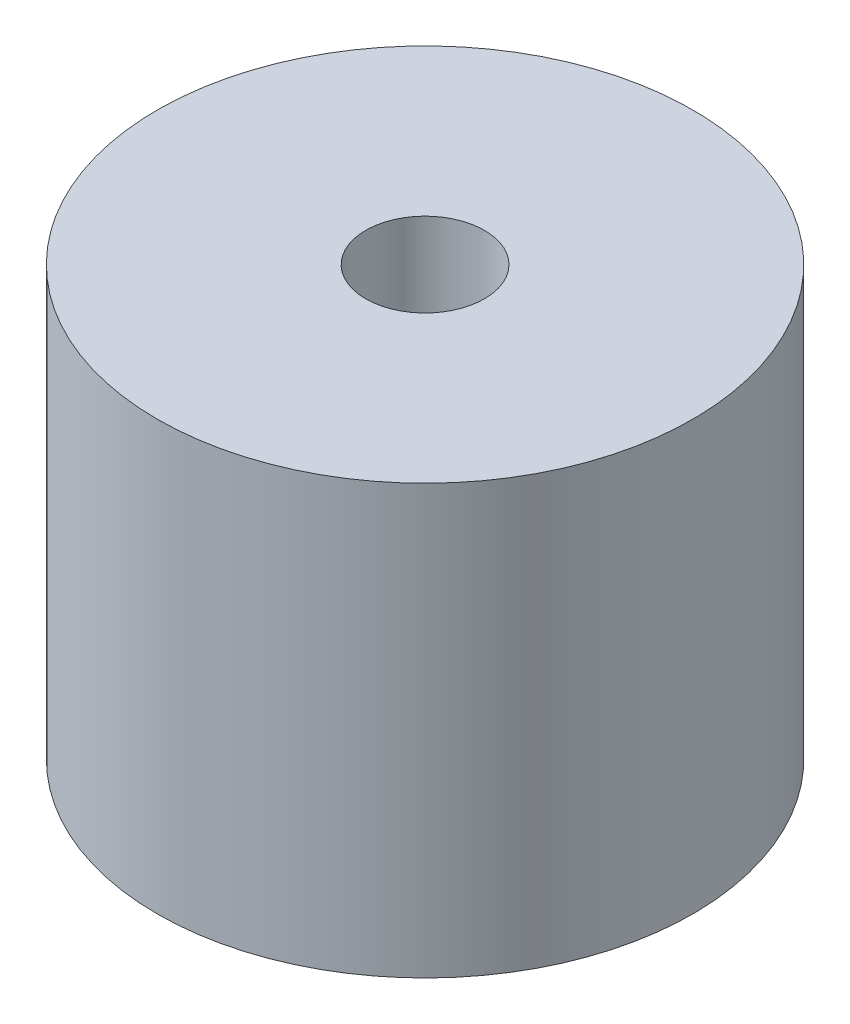
SolidWorks part; units mm, degrees
ref_plane "Front Plane" through (0, 0, 0) normal (0, 0, 1) x (1, 0, 0)
ref_plane "Top Plane" through (0, 0, 0) normal (0, 1, 0) x (1, 0, 0)
ref_plane "Right Plane" through (0, 0, 0) normal (1, 0, 0) x (0, 0, -1)
sketch "Sketch1" plane through (0, 0, 0) normal (0, 1, 0) x (1, 0, 0)
  circle A0 centre (0, 0) radius 6
  dimension "D1" = 12
extrude "Boss-Extrude1" add sketch "Sketch1" along normal blind 9.6
sketch "Sketch2" plane through (0, 9.6, 0) normal (0, 1, 0) x (1, 0, 0)
  circle A0 centre (0, 0) radius 1.33
  dimension "D1" = 2.66
extrude "Cut-Extrude1" cut sketch "Sketch2" against normal blind 3
sketch "Sketch3" plane through (0, 6.6, 0) normal (0, 1, 0) x (1, 0, 0)
  circle A0 centre (0, 0) radius 5
  dimension "D1" = 10
extrude "Cut-Extrude2" cut sketch "Sketch3" along normal blind 1
sketch "Sketch4" plane through (0, 0, 0) normal (0, -1, 0) x (1, 0, 0)
  line L0 (-6, 0) -> (6, 0) construction
  line L1 (0, 6) -> (0, -6) construction
  circle A0 centre (0, 0) radius 6 construction
  circle A1 centre (-3.75, 0) radius 0.3
  circle A2 centre (3.75, 0) radius 0.3
  dimension "D1" = 0.6
  dimension "D2" = 7.5
extrude "Boss-Extrude2" add sketch "Sketch4" along normal blind 1
